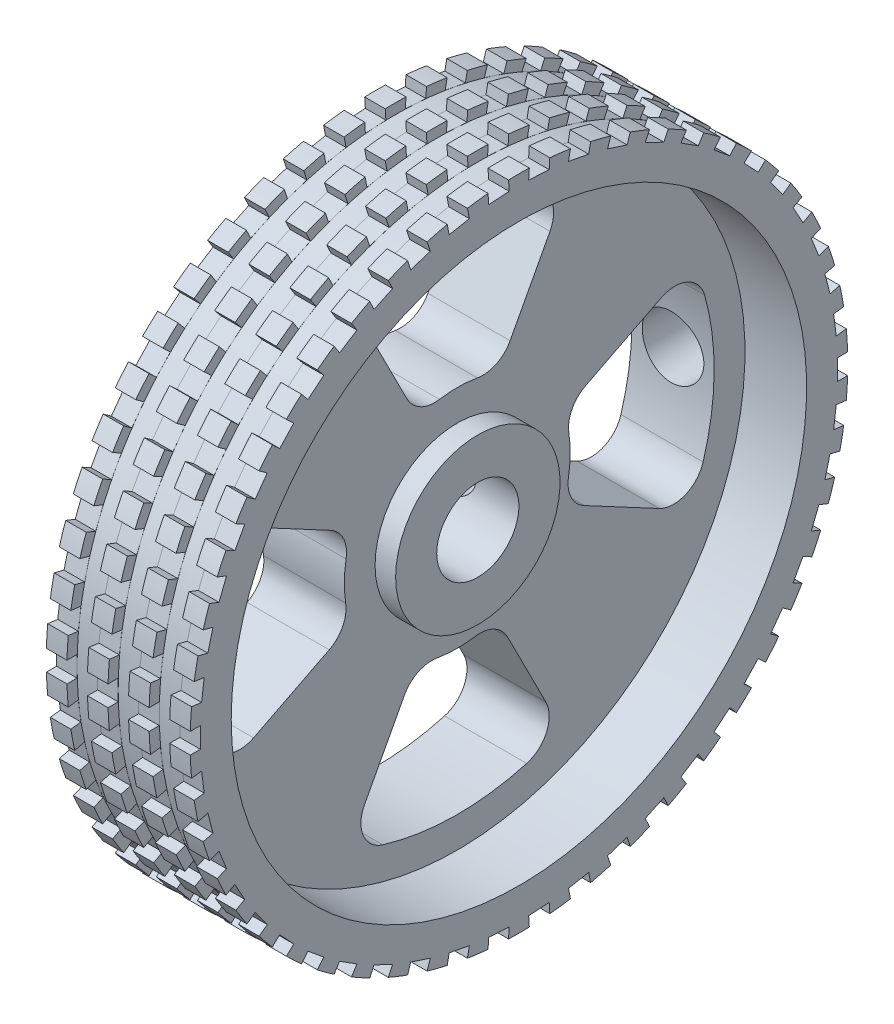
SolidWorks part; units mm, degrees
ref_plane "Front Plane" through (0, 0, 0) normal (0, 0, 1) x (1, 0, 0)
ref_plane "Top Plane" through (0, 0, 0) normal (0, 1, 0) x (1, 0, 0)
ref_plane "Right Plane" through (0, 0, 0) normal (1, 0, 0) x (0, 0, -1)
sketch "Sketch1" plane through (0, 0, 0) normal (0, 0, 1) x (1, 0, 0)
  line L0 (0, 16) -> (7, 16)
  line L2 (0, 2) -> (0, 16)
  line L4 (4, 4) -> (4, 14)
  line L7 (4, 14) -> (7, 14)
  line L8 (7, 16) -> (7, 14)
  line L11 (4, 4) -> (5, 4)
  line L12 (5, 2) -> (5, 4)
  line L13 (0, 2) -> (5, 2)
  line L14 (0, 0) -> (8.8457, 0) construction
  point P10 (5.5, 14)
  dimension "D1" = 7
  dimension "D2" = 5
  dimension "D3" = 4
  dimension "D4" = 32
  dimension "D5" = 28
  dimension "D6" = 8
  dimension "D7" = 4
revolve "Revolve1" add sketch "Sketch1" angle 360 about L14
sketch "Sketch3" plane through (0, 0, 0) normal (0, 1, 0) x (1, 0, 0)
  line L0 (2, 0) -> (2, 16)
  line L1 (2, 16) -> (3.5, 16)
  line L2 (3.5, 16) -> (3.5, 11.5)
  line L3 (3.5, 11.5) -> (2.9, 11.5)
  line L4 (2.9, 11.5) -> (2.9, 0)
  line L5 (2.9, 0) -> (2, 0)
  line L6 (0, 16) -> (0, -16) construction
  line L7 (7, 16) -> (0, 16) construction
  line L9 (2, 0) -> (2, 20.8258) construction
  dimension "D1" = 4.5
  dimension "D2" = 2
  dimension "D3" = 3
  dimension "D4" = 1.8
revolve "Cut-Revolve1" cut sketch "Sketch3" angle 360 about L9
sketch "Sketch4" plane through (4, 0, 0) normal (1, 0, 0) x (0, 0, -1)
  line L0 (-1.8989, 5.1618) -> (-5.077, 11.4225)
  line L1 (2.0042, 5.1219) -> (5.3098, 11.3162)
  circle A0 centre (0, 0) radius 5.5 construction
  arc A1 (-1.8989, 5.1618) -> (2.0042, 5.1219) centre (0, 0) cw
  arc A2 (-5.077, 11.4225) -> (5.3098, 11.3162) centre (0, 0) cw
  dimension "D1" = 11
  dimension "D2" = 12.5
  dimension "D3" = 55
extrude "Cut-Extrude1" cut sketch "Sketch4" against normal through all
fillet "Fillet1" radius 1.5 4 edges at (2, 5.1219, -2.0042) (2, 5.1618, 1.8989) (2, 11.3162, -5.3098) (2, 11.4225, 5.077)
pattern_circular "CirPattern1" count 4 over 360 about axis through (0, 0, 0) along (1, 0, 0) of "Cut-Extrude1", "Fillet1"
sketch "Sketch5" plane through (0, 0, 0) normal (0, 0, 1) x (1, 0, 0)
  line L0 (0, 0) -> (8.9998, 0) construction
  line L1 (7, 16) -> (0, 16) construction
  line L2 (1, 16) -> (2, 16)
  line L3 (1, 16) -> (1, 15.5)
  line L4 (1, 15.5) -> (2, 15.5)
  line L5 (2, 16) -> (2, 15.5)
  line L6 (0, 16) -> (0, -16) construction
  dimension "D1" = 1
  dimension "D2" = 0.5
  dimension "D3" = 1
revolve "Cut-Revolve2" cut sketch "Sketch5" angle 360 about L0
sketch "Sketch6" plane through (0, 0, 0) normal (1, 0, 0) x (0, 0, -1)
  line L0 (0, 0) -> (18.3796, 0) construction
  line L10 (15.5, 0.5) -> (16, 0.5)
  line L11 (15.5, 0.5) -> (15.5, -0.5)
  line L12 (15.5, -0.5) -> (16, -0.5)
  line L13 (16, 0.5) -> (16, -0.5)
  line L14 (15.5, 0.5) -> (16, -0.5) construction
  line L15 (15.5, -0.5) -> (16, 0.5) construction
  circle A0 centre (0, 0) radius 16 construction
  point P3 (15.75, 0)
  dimension "D1" = 0.5
  dimension "D2" = 1
extrude "Cut-Extrude5" cut sketch "Sketch6" along normal through all
pattern_circular "CirPattern2" count 50 over 360 about axis through (0, 0, 0) along (1, 0, 0) of "Cut-Extrude5"
pattern_linear "LPattern1" count 3 spacing 2 along (1, 0, 0) of "Cut-Revolve2"
